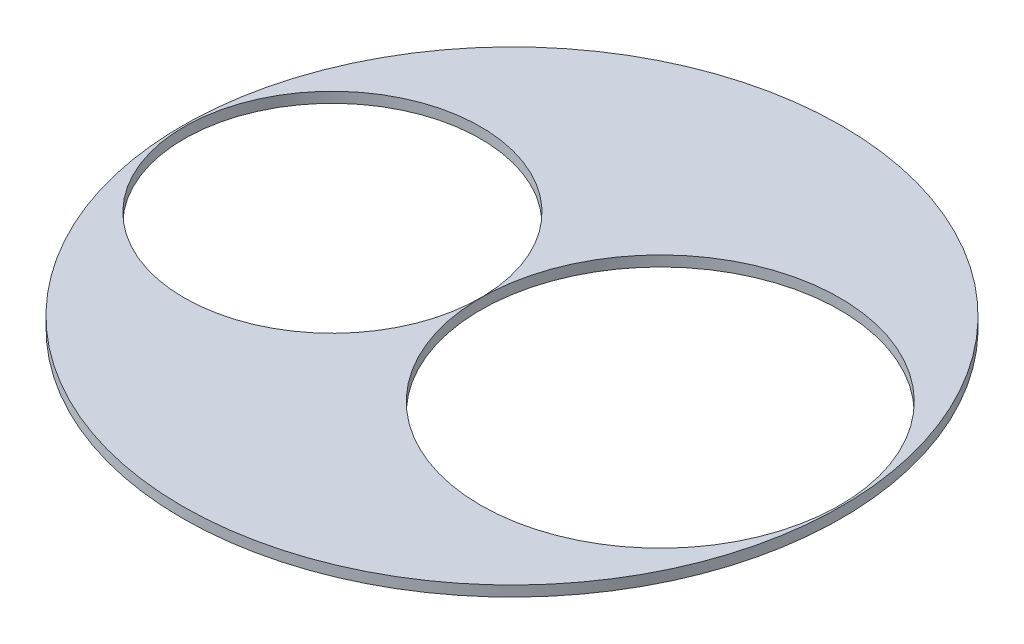
SolidWorks part; units mm, degrees
material "7075-T6 (SN)"
ref_plane "Front Plane" through (0, 0, 0) normal (0, 0, 1) x (1, 0, 0)
ref_plane "Top Plane" through (0, 0, 0) normal (0, 1, 0) x (1, 0, 0)
ref_plane "Right Plane" through (0, 0, 0) normal (1, 0, 0) x (0, 0, -1)
sketch "Sketch1" plane through (0, 0, 0) normal (0, 1, 0) x (1, 0, 0)
  circle A0 centre (0, 0) radius 1200
  circle A1 centre (539.876, 0) radius 654.05
  circle A2 centre (-653.9494, 0) radius 539.75
  dimension "D1" = 2400
  dimension "D2" = 1308.1
  dimension "D3" = 1079.5
  dimension "D4" = 1193.8254
extrude "Boss-Extrude1" add sketch "Sketch1" along normal blind 38.1
